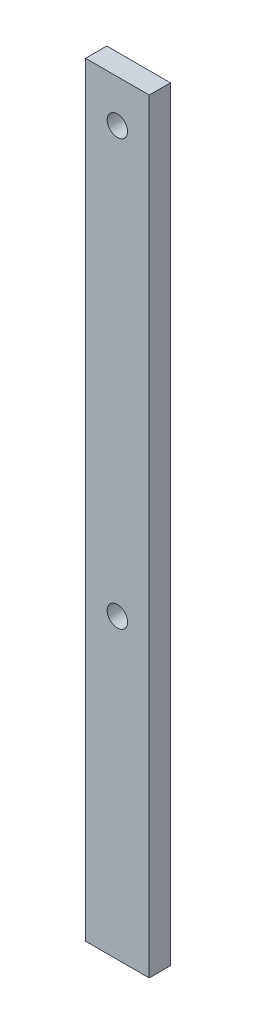
SolidWorks part; units mm, degrees
ref_plane "Front Plane" through (0, 0, 0) normal (0, 0, 1) x (1, 0, 0)
ref_plane "Top Plane" through (0, 0, 0) normal (0, 1, 0) x (1, 0, 0)
ref_plane "Right Plane" through (0, 0, 0) normal (1, 0, 0) x (0, 0, -1)
sketch "Sketch1" plane through (0, 0, 0) normal (0, 0, 1) x (1, 0, 0)
  line L1 (0, 0) -> (19.05, 0)
  line L2 (0, 0) -> (0, 228.6)
  line L3 (0, 228.6) -> (19.05, 228.6)
  line L4 (19.05, 0) -> (19.05, 228.6)
  dimension "D1" = 228.6
  dimension "D2" = 19.05
extrude "Boss-Extrude1" add sketch "Sketch1" along normal blind 6.35
sketch "Sketch2" plane through (0, 0, 6.35) normal (0, 0, 1) x (1, 0, 0)
  line L0 (19.05, 0) -> (19.05, 228.6) construction
  line L1 (19.05, 228.6) -> (0, 228.6) construction
  line L2 (0, 0) -> (19.05, 0) construction
  circle A0 centre (9.525, 215.9) radius 3.048
  circle A1 centre (9.525, 88.9) radius 3.048
  dimension "D3" = 6.096
  dimension "D6" = 6.096
  dimension "D1" = 9.525
  dimension "D2" = 12.7
  dimension "D4" = 9.525
  dimension "D5" = 88.9
extrude "Cut-Extrude1" cut sketch "Sketch2" against normal blind 6.35
